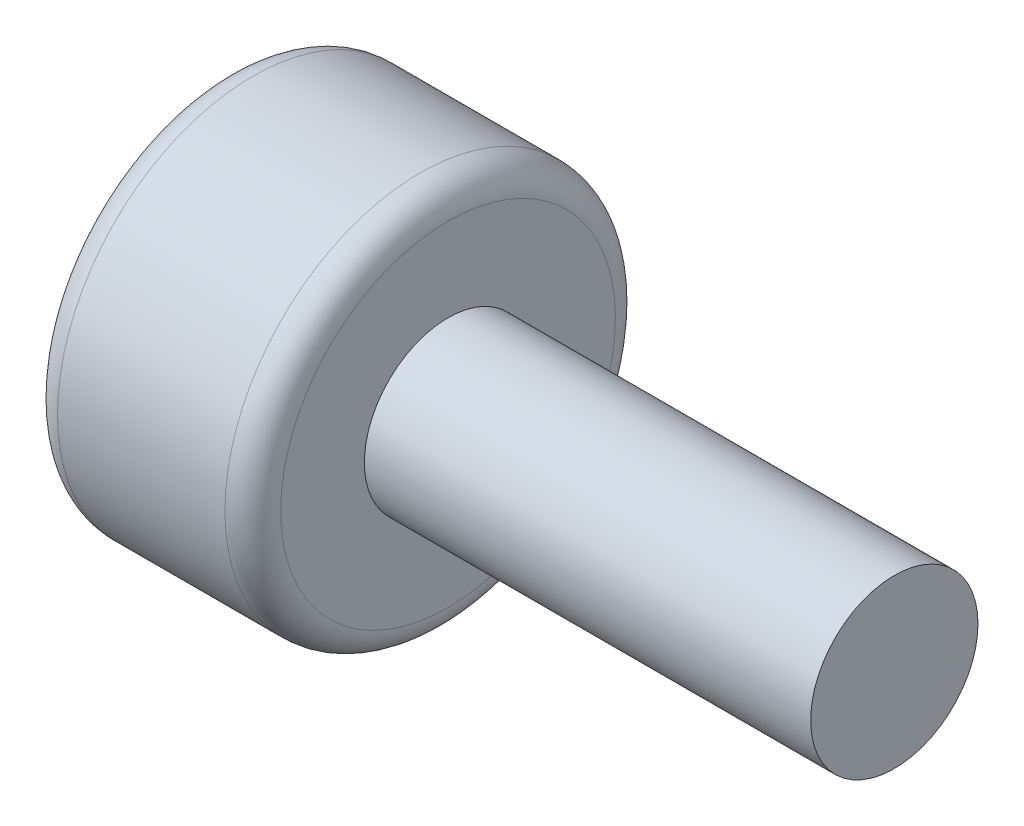
SolidWorks part; units mm, degrees
ref_plane "Front Plane" through (0, 0, 0) normal (0, 0, 1) x (1, 0, 0)
ref_plane "Top Plane" through (0, 0, 0) normal (0, 1, 0) x (1, 0, 0)
ref_plane "Right Plane" through (0, 0, 0) normal (1, 0, 0) x (0, 0, -1)
sketch "Sketch1" plane through (0, 0, 0) normal (1, 0, 0) x (0, 0, -1)
  circle A0 centre (0, 0) radius 3.5
extrude "Boss-Extrude1" add sketch "Sketch1" along normal blind 4
sketch "Sketch2" plane through (4, 0, 0) normal (1, 0, 0) x (0, 0, -1)
  circle A0 centre (0, 0) radius 1.5
extrude "Boss-Extrude2" add sketch "Sketch2" along normal blind 8
sketch "Sketch3" plane through (0, 0, 0) normal (-1, 0, 0) x (0, 0, 1)
  line L1 (0, 1.7321) -> (-1.5, 0.866)
  line L2 (-1.5, 0.866) -> (-1.5, -0.866)
  line L3 (-1.5, -0.866) -> (0, -1.7321)
  line L4 (0, -1.7321) -> (1.5, -0.866)
  line L5 (1.5, -0.866) -> (1.5, 0.866)
  line L6 (1.5, 0.866) -> (0, 1.7321)
  circle A0 centre (0, 0) radius 1.5 construction
extrude "Cut-Extrude1" cut sketch "Sketch3" against normal blind 2
fillet "Fillet1" radius 0.5 2 edges at (0, 0, -3.5) (4, 0, -3.5)
